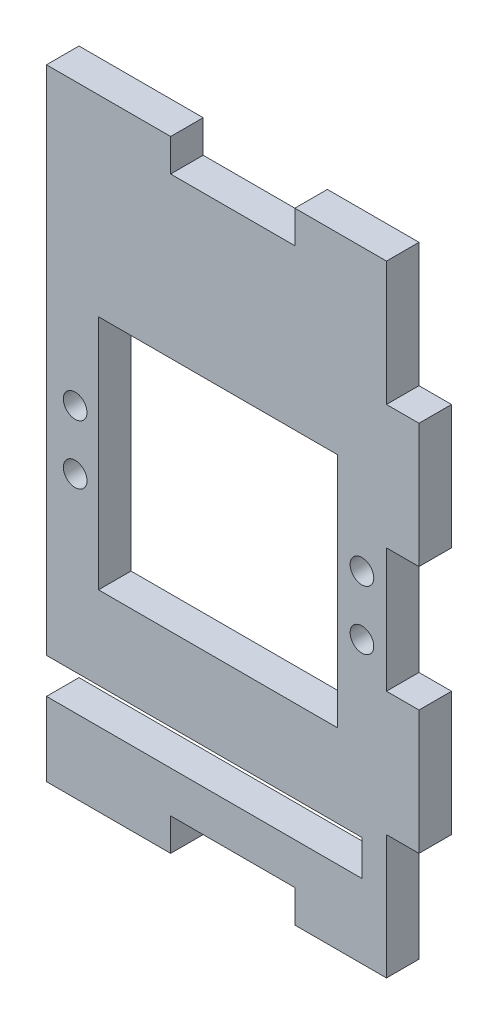
SolidWorks part; units mm, degrees
ref_plane "Alzado" through (0, 0, 0) normal (0, 0, 1) x (1, 0, 0)
ref_plane "Planta" through (0, 0, 0) normal (0, 1, 0) x (1, 0, 0)
ref_plane "Vista lateral" through (0, 0, 0) normal (1, 0, 0) x (0, 0, -1)
sketch "Croquis2" plane through (0, 0, 0) normal (0, 0, 1) x (1, 0, 0)
  line L12 (-10.5, 50) -> (-10.5, -34)
  line L13 (-10.5, -50) -> (10.5, -50)
  line L14 (10.5, -50) -> (10.5, -47)
  line L15 (10.5, -47) -> (31.5, -47)
  line L16 (31.5, -47) -> (31.5, -50)
  line L17 (31.5, -50) -> (47, -50)
  line L18 (47, -50) -> (47, -31.5)
  line L19 (47, -31.5) -> (50, -31.5)
  line L20 (50, -31.5) -> (50, -10.5)
  line L21 (50, -10.5) -> (47, -10.5)
  line L22 (47, -10.5) -> (47, 10.5)
  line L23 (47, 10.5) -> (50, 10.5)
  line L24 (50, 10.5) -> (50, 31.5)
  line L25 (50, 31.5) -> (47, 31.5)
  line L26 (47, 31.5) -> (47, 50)
  line L27 (47, 50) -> (31.5, 50)
  line L28 (31.5, 50) -> (31.5, 47)
  line L29 (31.5, 47) -> (10.5, 47)
  line L30 (10.5, 47) -> (10.5, 50)
  line L31 (10.5, 50) -> (-10.5, 50)
  line L36 (-10.5, -34) -> (42.85, -34)
  line L37 (42.85, -34) -> (42.85, -40)
  line L38 (-0.4361, 0) -> (46.5639, 0) construction
  line L39 (-1.7, 20) -> (38.7, 20)
  line L40 (-1.7, 20) -> (-1.7, -20)
  line L41 (-1.7, -20) -> (38.7, -20)
  line L42 (38.7, 20) -> (38.7, -20)
  line L43 (42.85, -40) -> (-10.5, -40)
  line L44 (-10.5, -40) -> (-10.5, -50)
  circle A5 centre (42.85, 5) radius 2
  circle A6 centre (-5.65, 5) radius 2
  circle A7 centre (42.85, -5) radius 2
  circle A8 centre (-5.65, -5) radius 2
  dimension "D7" = 4
  dimension "D2" = 100
  dimension "D3" = 40.4
  dimension "D4" = 40
  dimension "D5" = 8.3
  dimension "D6" = 30
  dimension "D8" = 5
  dimension "D9" = 4.15
  dimension "D10" = 48.5
  dimension "D11" = 6
  dimension "D12" = 10
extrude "Saliente-Extruir1" add sketch "Croquis2" along normal blind 5.5
sketch "Croquis3" plane through (50, 0, 0) normal (1, 0, 0) x (0, 0, -1)
  line L0 (0, -31.5) -> (0, -10.5) construction
  line L1 (0, -10.5) -> (-5.5, -10.5) construction
  line L2 (-5.5, -10.5) -> (-5.5, -31.5) construction
  line L3 (-5.5, -31.5) -> (0, -31.5) construction
  line L4 (0, 10.5) -> (0, 31.5) construction
  line L5 (0, 31.5) -> (-5.5, 31.5) construction
  line L6 (-5.5, 31.5) -> (-5.5, 10.5) construction
  line L7 (-5.5, 10.5) -> (0, 10.5) construction
  line L8 (0, -31.5) -> (0, -10.5)
  line L9 (0, -10.5) -> (-5.5, -10.5)
  line L10 (-5.5, -10.5) -> (-5.5, -31.5)
  line L11 (-5.5, -31.5) -> (0, -31.5)
  line L12 (0, 10.5) -> (0, 31.5)
  line L13 (0, 31.5) -> (-5.5, 31.5)
  line L14 (-5.5, 31.5) -> (-5.5, 10.5)
  line L15 (-5.5, 10.5) -> (0, 10.5)
extrude "Saliente-Extruir2" add sketch "Croquis3" along normal blind 2.5
sketch "Croquis4" plane through (0, 50, 0) normal (0, 1, 0) x (1, 0, 0)
  line L0 (47, 0) -> (31.5, 0) construction
  line L1 (31.5, 0) -> (31.5, -5.5) construction
  line L2 (31.5, -5.5) -> (47, -5.5) construction
  line L3 (47, -5.5) -> (47, 0) construction
  line L4 (10.5, 0) -> (-10.5, 0) construction
  line L5 (-10.5, 0) -> (-10.5, -5.5) construction
  line L6 (-10.5, -5.5) -> (10.5, -5.5) construction
  line L7 (10.5, -5.5) -> (10.5, 0) construction
  line L8 (47, 0) -> (31.5, 0)
  line L9 (31.5, 0) -> (31.5, -5.5)
  line L10 (31.5, -5.5) -> (47, -5.5)
  line L11 (47, -5.5) -> (47, 0)
  line L12 (10.5, 0) -> (-10.5, 0)
  line L13 (-10.5, 0) -> (-10.5, -5.5)
  line L14 (-10.5, -5.5) -> (10.5, -5.5)
  line L15 (10.5, -5.5) -> (10.5, 0)
extrude "Saliente-Extruir3" add sketch "Croquis4" along normal blind 2.5
sketch "Croquis5" plane through (0, -50, 0) normal (0, -1, 0) x (1, 0, 0)
  line L0 (31.5, 0) -> (47, 0) construction
  line L1 (47, 0) -> (47, 5.5) construction
  line L2 (47, 5.5) -> (31.5, 5.5) construction
  line L3 (31.5, 5.5) -> (31.5, 0) construction
  line L4 (-10.5, 0) -> (10.5, 0) construction
  line L5 (10.5, 0) -> (10.5, 5.5) construction
  line L6 (10.5, 5.5) -> (-10.5, 5.5) construction
  line L7 (-10.5, 5.5) -> (-10.5, 0) construction
  line L8 (31.5, 0) -> (47, 0)
  line L9 (47, 0) -> (47, 5.5)
  line L10 (47, 5.5) -> (31.5, 5.5)
  line L11 (31.5, 5.5) -> (31.5, 0)
  line L12 (-10.5, 0) -> (10.5, 0)
  line L13 (10.5, 0) -> (10.5, 5.5)
  line L14 (10.5, 5.5) -> (-10.5, 5.5)
  line L15 (-10.5, 5.5) -> (-10.5, 0)
extrude "Saliente-Extruir4" add sketch "Croquis5" along normal blind 2.5
